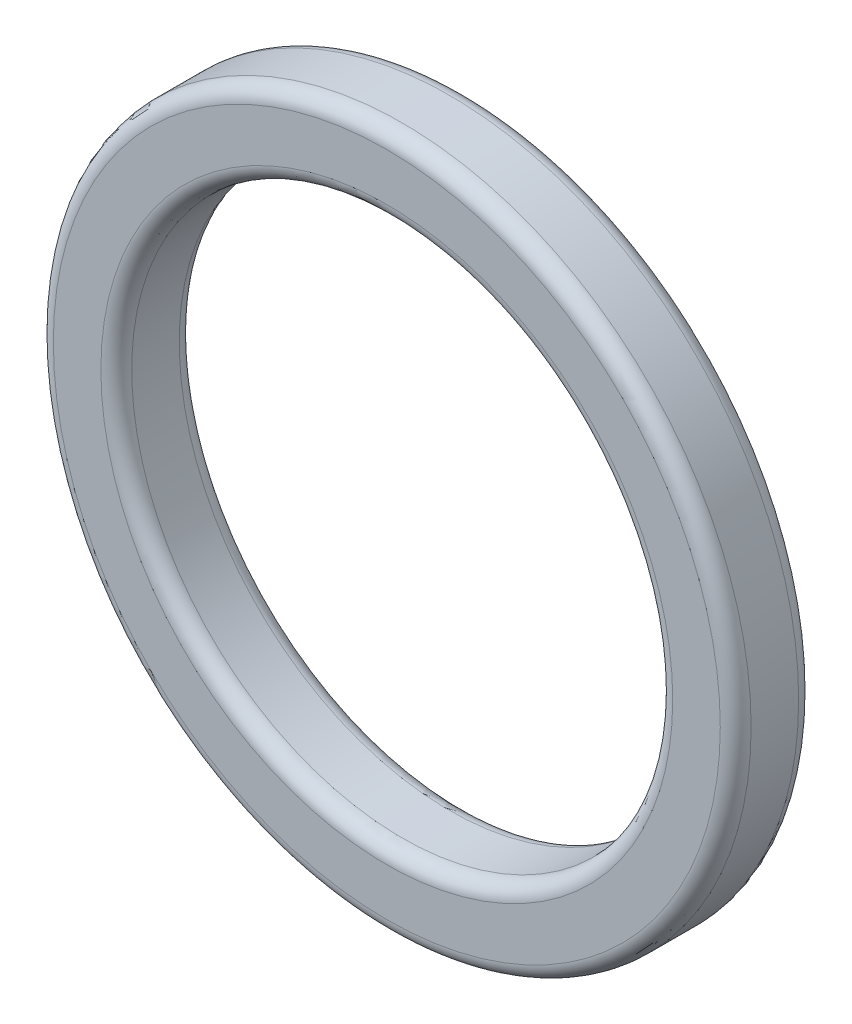
SolidWorks part; units mm, degrees
ref_plane "Front Plane" through (0, 0, 0) normal (0, 0, 1) x (1, 0, 0)
ref_plane "Top Plane" through (0, 0, 0) normal (0, 1, 0) x (1, 0, 0)
ref_plane "Right Plane" through (0, 0, 0) normal (1, 0, 0) x (0, 0, -1)
sketch "Sketch1" plane through (0, 0, 0) normal (0, 0, 1) x (1, 0, 0)
  line L0 (39.7849, 28.4386) -> (39.7849, -9.1693) construction
  circle A2 centre (39.7849, 9.6346) radius 20.0728
  point P2 (39.7849, 9.6346)
extrude "Extrude-Thin1" add sketch "Sketch1" along normal blind 5.08 thin thin type mid plane wall 5.08
fillet "Fillet1" radius 1 4 edges at (57.3177, 9.6346, 0) (62.3977, 9.6346, 0) (57.3177, 9.6346, 5.08) (62.3977, 9.6346, 5.08)
